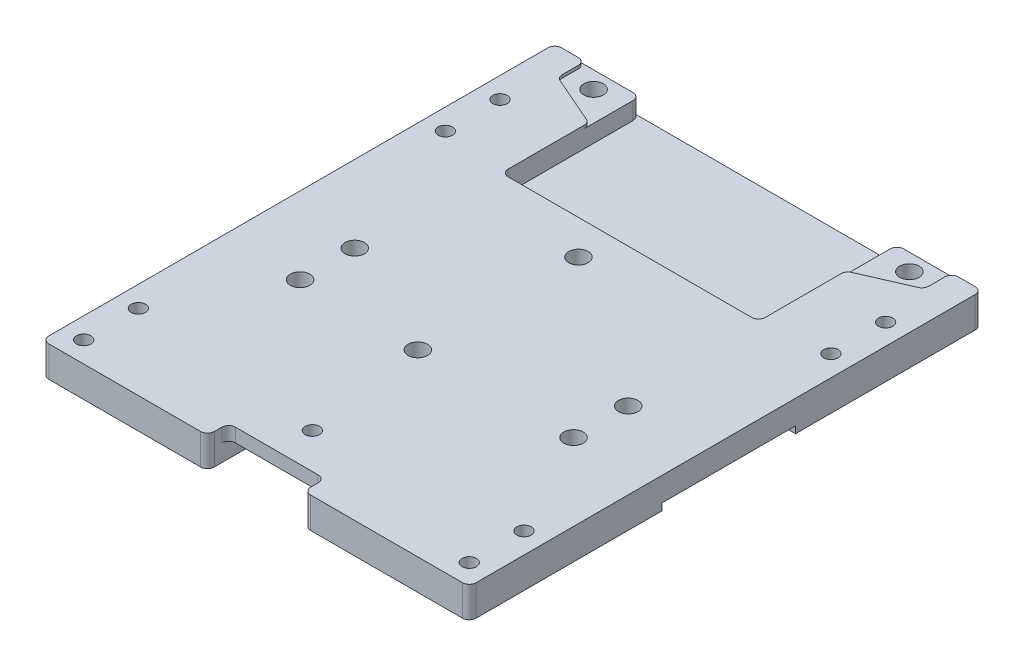
SolidWorks part; units mm, degrees
ref_plane "Front Plane" through (0, 0, 0) normal (0, 0, 1) x (1, 0, 0)
ref_plane "Top Plane" through (0, 0, 0) normal (0, 1, 0) x (1, 0, 0)
ref_plane "Right Plane" through (0, 0, 0) normal (1, 0, 0) x (0, 0, -1)
sketch "Sketch1" plane through (0, 0, 0) normal (0, 1, 0) x (1, 0, 0)
  line L0 (6.1, 127.9) -> (6.1, 6.1) construction
  line L1 (6.1, 6.1) -> (118.9, 6.1) construction
  line L2 (118.9, 6.1) -> (118.9, 127.9) construction
  line L3 (118.9, 127.9) -> (6.1, 127.9) construction
  line L4 (6.1, 111.9) -> (118.9, 111.9) construction
  line L5 (6.1, 22.1) -> (118.9, 22.1) construction
  line L6 (0, 150) -> (125, 0) construction
  line L7 (76.6, 0) -> (125, 0)
  line L13 (6.1, 108.2) -> (118.9, 108.2) construction
  line L14 (118.9, 47.9) -> (6.1, 47.9) construction
  line L15 (0, 0) -> (48.4, 0)
  line L16 (0, 0) -> (0, 150)
  line L17 (0, 150) -> (125, 150)
  line L18 (125, 0) -> (125, 150)
  line L19 (48.4, 0) -> (48.4, -15)
  line L20 (48.4, -15) -> (76.6, -15)
  line L21 (76.6, 0) -> (76.6, -15)
  line L22 (54.5, -8.9) -> (70.5, -8.9) construction
  line L24 (22.5, 37) -> (102.5, 37) construction
  line L25 (22.5, 37) -> (22.5, 69) construction
  line L26 (22.5, 69) -> (102.5, 69) construction
  line L27 (102.5, 37) -> (102.5, 69) construction
  circle A0 centre (6.1, 127.9) radius 2.1
  circle A1 centre (6.1, 111.9) radius 2.1
  circle A2 centre (118.9, 127.9) radius 2.1
  circle A3 centre (118.9, 111.9) radius 2.1
  circle A4 centre (118.9, 22.1) radius 2.1
  circle A5 centre (118.9, 6.1) radius 2.1
  circle A6 centre (6.1, 6.1) radius 2.1
  circle A7 centre (6.1, 22.1) radius 2.1
  circle A16 centre (54.5, -8.9) radius 2.1
  circle A17 centre (70.5, -8.9) radius 2.1
  circle A18 centre (62.5, -0.9) radius 2.1
  circle A19 centre (102.5, 53) radius 2.85
  circle A20 centre (22.5, 37) radius 2.1 construction
  circle A21 centre (22.5, 69) radius 2.85
  circle A22 centre (102.5, 69) radius 2.85
  circle A23 centre (22.5, 53) radius 2.85
  point P20 (62.5, 150)
  point P24 (62.5, 127.9)
  point P52 (62.5, -8.9)
  point P53 (62.5, -15)
  point P56 (62.5, 37)
  dimension "D1" = 4.2
  dimension "D20" = 4.2
  dimension "D22" = 5.7
  dimension "D8" = 4.2
  dimension "D3" = 16
  dimension "D9" = 3.7
  dimension "D11" = 25.8
  dimension "D4" = 4
  dimension "D5" = 20
  dimension "D12" = 125
  dimension "D13" = 150
  dimension "D14" = 60.3
  dimension "D15" = 195.2562
  dimension "D16" = 15
  dimension "D17" = 28.2
  dimension "D18" = 16
  dimension "D19" = 4
  dimension "D21" = 8
  dimension "D23" = 80
  dimension "D24" = 39.1
  dimension "D25" = 16
  dimension "D26" = 16
  dimension "D7" = 16
  dimension "D6" = 4
  dimension "wheelbase" = 105.8
extrude "Boss-Extrude1" add sketch "Sketch1" along normal blind 9
sketch "Sketch2" plane through (0, 9, 0) normal (0, 1, 0) x (1, 0, 0)
  line L1 (76.6, -15) -> (76.6, 0) construction
  line L2 (48.4, -15) -> (76.6, -15) construction
  line L3 (48.4, 0) -> (48.4, -15) construction
  line L4 (76.6, -15) -> (76.6, 0)
  line L5 (48.4, -15) -> (76.6, -15)
  line L6 (48.4, 0) -> (48.4, -15)
  line L7 (76.6, 0) -> (76.6, 6.2)
  line L8 (76.6, 6.2) -> (48.4, 6.2)
  line L9 (48.4, 6.2) -> (48.4, 0)
  circle A0 centre (62.5, -0.9) radius 2.1 construction
  dimension "D1" = 5
extrude "Cut-Extrude1" cut sketch "Sketch2" against normal blind 4
sketch "Sketch10" plane through (0, 0, 0) normal (0, 1, 0) x (1, 0, 0)
  line L0 (48.4, -15) -> (48.4, 27)
  line L1 (48.4, 27) -> (76.6, 27)
  line L2 (76.6, 27) -> (76.6, -15)
  line L3 (76.6, -15) -> (48.4, -15)
  dimension "D1" = 42
extrude "Cut-Extrude8" cut sketch "Sketch10" against normal up to surface (5 mm away)
sketch "Sketch11" plane through (0, 5, 0) normal (0, -1, 0) x (1, 0, 0)
  line L0 (76.6, -6.2) -> (48.4, -6.2) construction
  line L1 (48.4, -6.2) -> (48.4, -27) construction
  line L2 (76.6, -27) -> (48.4, -27) construction
  line L3 (48.4, -27) -> (48.4, 0) construction
  circle A0 centre (62.5, -16.6) radius 2.1
  point P4 (62.5, -6.2)
  point P12 (48.4, -16.6)
  dimension "D1" = 4.2
extrude "Cut-Extrude9" cut sketch "Sketch11" against normal through all
ref_plane "Midplane_lengthwise" through (62.5, 0, 0) normal (-1, 0, 0) x (0, 0, 1)
ref_plane "Midplane_sideways" through (0, 0, -75) normal (0, 0, -1) x (-1, 0, 0)
sketch "Sketch3" plane through (0, 0, 0) normal (0, -1, 0) x (1, 0, 0)
  line L0 (0, -56.45) -> (27, -56.45)
  line L1 (27, -56.45) -> (27, -46.45)
  line L2 (27, -46.45) -> (86.5, -46.45)
  line L3 (86.5, -46.45) -> (86.5, -56.45)
  line L4 (86.5, -56.45) -> (125, -56.45)
  line L5 (125, 0) -> (125, -150) construction
  line L6 (125, -56.45) -> (125, -95.45)
  line L8 (125, -95.45) -> (86.5, -95.45)
  line L9 (86.5, -95.45) -> (86.5, -105.45)
  line L10 (86.5, -105.45) -> (27, -105.45)
  line L11 (27, -105.45) -> (27, -95.45)
  line L12 (27, -95.45) -> (0, -95.45)
  line L13 (0, -150) -> (0, 0) construction
  line L14 (0, -95.45) -> (0, -56.45)
extrude "Cut-Extrude2" cut sketch "Sketch3" against normal blind 2
sketch "Sketch5" plane through (0, 2, 0) normal (0, -1, 0) x (1, 0, 0)
  circle A0 centre (57.5, -52.45) radius 2.85
  circle A1 centre (57.5, -99.45) radius 2.85
  circle A2 centre (22.5, -69) radius 2.85 construction
extrude "Cut-Extrude3" cut sketch "Sketch5" against normal through all
sketch "Sketch7" plane through (0, 9, 0) normal (0, 1, 0) x (1, 0, 0)
  line L0 (125, 150) -> (0, 150) construction
  line L12 (125, 150) -> (0, 150) construction
  line L13 (24.9, 150) -> (100.1, 150)
  line L17 (24.9, 150) -> (24.9, 109.5)
  line L18 (24.9, 109.5) -> (100.1, 109.5)
  line L19 (100.1, 150) -> (100.1, 109.5)
  line L20 (0, 150) -> (0, 0) construction
  point P6 (62.5, 150)
  point P9 (62.5, 150)
  dimension "D1" = 24.9
  dimension "D2" = 40.5
extrude "Cut-Extrude5" cut sketch "Sketch7" against normal blind 6
sketch "Sketch12" plane through (0, 9, 0) normal (0, 1, 0) x (1, 0, 0)
  line L0 (16.3, 145.05) -> (108.7, 145.05) construction
  line L1 (100.1, 150) -> (24.9, 150) construction
  line L3 (0, 150) -> (0, 0) construction
  line L4 (24.9, 150) -> (0, 150) construction
  circle A0 centre (16.3, 145.05) radius 2.85
  circle A1 centre (108.7, 145.05) radius 2.85
  point P3 (62.5, 145.05)
  point P6 (62.5, 150)
  dimension "D1" = 5.7
  dimension "D3" = 16.3
  dimension "D2" = 2.1
  dimension "D4" = 4.95
extrude "Cut-Extrude10" cut sketch "Sketch12" against normal through all
sketch "Sketch13" plane through (0, 9, 0) normal (0, 1, 0) x (1, 0, 0)
  line L0 (24.9, 135) -> (8.9, 142)
  line L1 (24.9, 150) -> (24.9, 109.5) construction
  line L2 (8.9, 142) -> (8.9, 150)
  line L3 (24.9, 150) -> (0, 150) construction
  line L4 (8.9, 150) -> (24.9, 150)
  line L5 (24.9, 150) -> (24.9, 135)
  line L6 (62.5, -850) -> (62.5, 49150) construction
  line L7 (100.1, 150) -> (24.9, 150) construction
  line L8 (100.1, 150) -> (100.1, 135)
  line L9 (116.1, 150) -> (100.1, 150)
  line L10 (116.1, 142) -> (116.1, 150)
  line L11 (100.1, 135) -> (116.1, 142)
  point P14 (62.5, 150)
  dimension "D1" = 16
  dimension "D2" = 8
  dimension "D3" = 15
extrude "Cut-Extrude11" cut sketch "Sketch13" against normal offset from surface (0.9 mm away) 8.1 up to face at (16.3, 0, -142.2)
fillet "Fillet1" radius 2 6 edges at (125, 4.5, -150) (0, 4.5, -150) (0, 4.5, 0) (125, 4.5, 0) (76.6, 7, -6.2) (48.4, 7, -6.2)
fillet "Fillet2" radius 2 2 edges at (76.6, 4.5, 0) (48.4, 4.5, 0)
fillet "Fillet3" radius 2 10 edges at (100.1, 8.55, -135) (116.1, 8.55, -142) (116.1, 8.55, -150) (8.9, 8.55, -150) (24.9, 8.55, -135) (8.9, 8.55, -142) (24.9, 5.55, -150) (100.1, 5.55, -150) (24.9, 6, -109.5) (100.1, 6, -109.5)
equation "\"width\"= 24"
equation "\"thk\"= 3"
equation "\"holesize\"= 4.2"
equation "\"holedistance\"= ( 20 + 12 ) / 2"
equation "\"threaded_hole\"= 3.9"
equation "\"fillet_radius\"= 2"
equation "\"ground_clearance\"= 25"
equation "\"tire_thk\"= 3"
equation "\"innerwheel_diam\" = \"wheel_diam\"-2*\"tire_thk\""
equation "\"innerwheel_thk\"= 8"
equation "\"wheel_diam\"= 2*(\"width\"/2+\"ground_clearance\")"
equation "\"coloursensor_holesize\"= 2.65"
equation "\"D3@Sketch1\" = \"holedistance\""
equation "\"D1@Sketch1\" = \"holesize\""
equation "\"D1@Boss-Extrude1\"=\"thk\""
equation "\"hole_to_edge\" = 4"
equation "\"D18@Sketch1\"=\"holedistance\""
equation "\"D20@Sketch1\"=\"holesize\""
equation "\"D21@Sketch1\"=\"holedistance\"/2"
equation "\"D1@Cut-Extrude1\"=\"thk\"+1"
equation "\"D25@Sketch1\"=\"holedistance\""
equation "\"D26@Sketch1\"=\"holedistance\""
equation "\"D8@Sketch1\"=\"holesize\""
equation "\"D7@Sketch1\"=\"holedistance\""
equation "\"D1@Fillet2\"=\"fillet_radius\""
equation "\"M4_insert_diam\"= 5.7"
equation "\"D1@Sketch11\"=\"holesize\""
equation "\"D1@Fillet1\"=\"fillet_radius\""
equation "\"D1@Sketch12\"=\"M4_insert_diam\""
